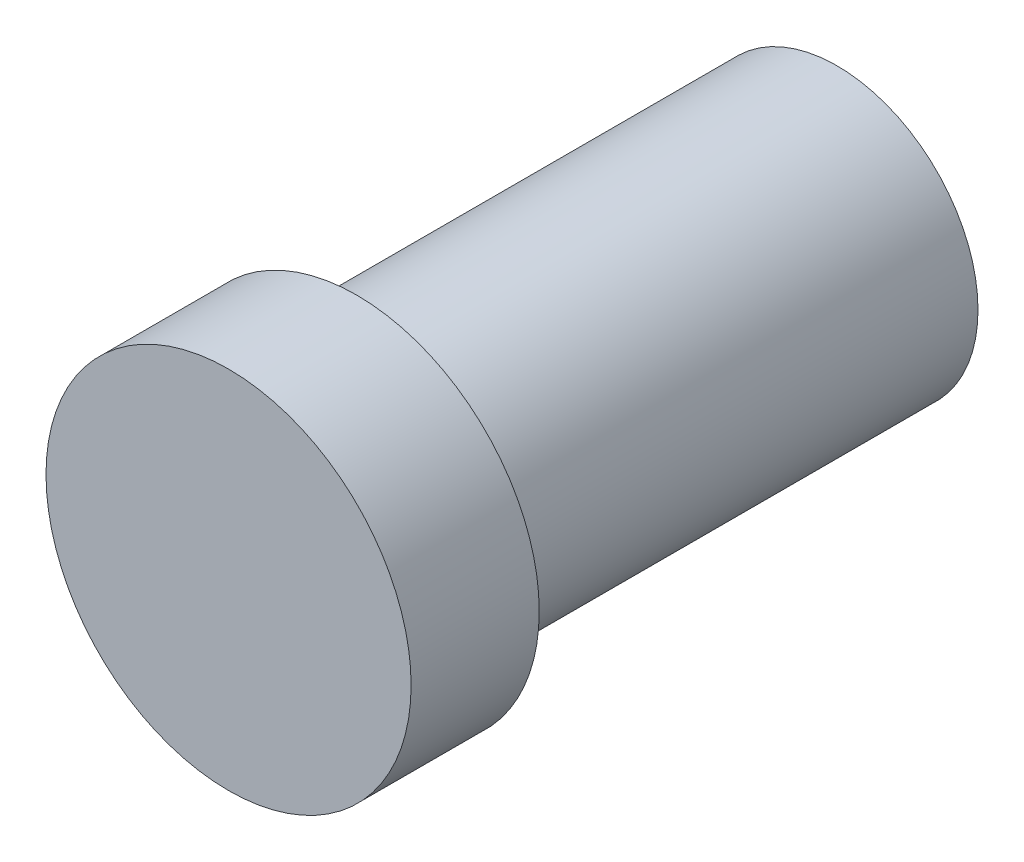
SolidWorks part; units mm, degrees
ref_plane "Front Plane" through (0, 0, 0) normal (0, 0, 1) x (1, 0, 0)
ref_plane "Top Plane" through (0, 0, 0) normal (0, 1, 0) x (1, 0, 0)
ref_plane "Right Plane" through (0, 0, 0) normal (1, 0, 0) x (0, 0, -1)
sketch "Sketch1" plane through (0, 0, 0) normal (0, 0, 1) x (1, 0, 0)
  circle A0 centre (0, 0) radius 22
  dimension "D1" = 44
extrude "Boss-Extrude1" add sketch "Sketch1" along normal blind 75
sketch "Sketch2" plane through (0, 0, 75) normal (0, 0, 1) x (1, 0, 0)
  circle A0 centre (0, 0) radius 28.5
  dimension "D1" = 57
extrude "Boss-Extrude2" add sketch "Sketch2" along normal blind 20
